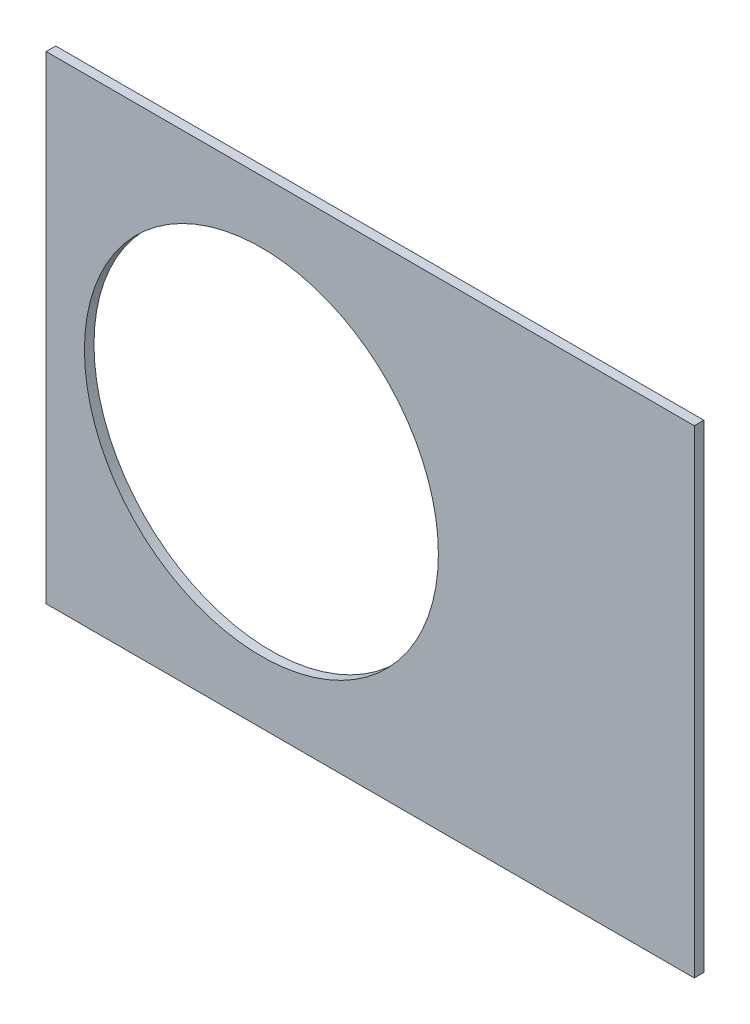
SolidWorks part; units mm, degrees
material "Copper"
ref_plane "Front Plane" through (0, 0, 0) normal (0, 0, 1) x (1, 0, 0)
ref_plane "Top Plane" through (0, 0, 0) normal (0, 1, 0) x (1, 0, 0)
ref_plane "Right Plane" through (0, 0, 0) normal (1, 0, 0) x (0, 0, -1)
sketch "Sketch1" plane through (0, 0, 0) normal (0, 0, 1) x (1, 0, 0)
  line L0 (0, 0) -> (320.3893, 0) construction
  line L1 (0, 0) -> (155.5285, 155.5285) construction
  line L2 (67.2115, 76.1917) -> (8.6967, 17.6769)
  line L3 (8.6967, 17.6769) -> (7.229, 14.1336)
  line L4 (101.4014, -6.35) -> (18.6489, -6.35)
  line L5 (15.1056, -4.8823) -> (18.6489, -6.35)
  line L6 (88.6729, 6.35) -> (27.8605, 6.35)
  line L9 (67.1914, 58.2111) -> (24.1905, 15.2102)
  line L10 (0, 0) -> (40.4486, 97.6516) construction
  line L11 (0, 0) -> (123.4567, -51.1374) construction
  line L18 (8.6967, 17.6769) -> (13.294, 8.6183) construction
  line L19 (18.6489, -6.35) -> (15.4943, 3.3063) construction
  line L20 (27.8605, 6.35) -> (27.7442, 6.7059) construction
  line L21 (24.1905, 15.2102) -> (24.3599, 14.8764) construction
  arc A0 (7.229, 14.1336) -> (15.1056, -4.8823) centre (0, 0) cw
  arc A1 (67.2115, 76.1917) -> (101.4014, -6.35) centre (0, 0) cw
  arc A2 (24.1905, 15.2102) -> (27.8605, 6.35) centre (0, 0) cw
  arc A3 (67.1914, 58.2111) -> (88.6729, 6.35) centre (0, 0) cw
  arc A8 (13.294, 8.6183) -> (15.4943, 3.3063) centre (0, 0) cw construction
  arc A9 (24.3599, 14.8764) -> (27.7442, 6.7059) centre (0, 0) cw construction
  dimension "D1" = 45
  dimension "D3" = 6.35
  dimension "D4" = 15.875
  dimension "D7" = 22.5
  dimension "D8" = 101.6
  dimension "D11" = 12.7
  dimension "D12" = 12.7
  dimension "D2" = 6.35
  dimension "D5" = 67.5
  dimension "D9" = 1.27
  dimension "D10" = 1.27
  dimension "D6" = 12.7
extrude "Boss-Extrude1" add sketch "Sketch1" along normal blind 0.254
sketch "Sketch2" plane through (0, 0, 0.254) normal (0, 0, 1) x (1, 0, 0)
  line L0 (0, 0) -> (101.6, 0) construction
  line L1 (0, 0) -> (71.842, 71.842) construction
  line L3 (0, 0) -> (22.225, 0) construction
  line L4 (0, 0) -> (15.7154, 15.7154) construction
  line L5 (0, 0) -> (95.25, 0) construction
  line L6 (0, 0) -> (92.0044, 24.6525) construction
  arc A0 (101.4014, -6.35) -> (67.2115, 76.1917) centre (0, 0) ccw construction
  circle A1 centre (22.225, 0) radius 4.699
  arc A2 (15.1056, -4.8823) -> (7.229, 14.1336) centre (0, 0) ccw construction
  circle A3 centre (36.195, 0) radius 4.699
  circle A4 centre (61.722, 0) radius 4.699
  circle A5 centre (75.692, 0) radius 4.699
  circle A6 centre (95.25, 0) radius 4.699
  circle A7 centre (15.7154, 15.7154) radius 4.699
  circle A8 centre (25.5937, 25.5937) radius 4.699
  circle A9 centre (43.644, 43.644) radius 4.699
  circle A10 centre (53.5223, 53.5223) radius 4.699
  circle A11 centre (92.0044, 24.6525) radius 4.699
  circle A12 centre (82.4889, 47.625) radius 4.699
  circle A13 centre (67.3519, 67.3519) radius 4.699
  dimension "D3" = 9.398
  dimension "D1" = 45
  dimension "D2" = 6.35
  dimension "D4" = 6.35
  dimension "D5" = 13.97
  dimension "D7" = 13.97
  dimension "D8" = 19.558
  dimension "D9" = 45
  dimension "D10" = 15
  dimension "D11" = 25.527
  dimension "D6" = 2
extrude "Cut-Extrude1" cut sketch "Sketch2" against normal through all
sketch "Sketch3" plane through (0, 0, 0.254) normal (0, 0, 1) x (1, 0, 0)
  line L0 (15.2664, 24.2467) -> (17.0625, 26.0427)
  line L1 (15.2664, 24.2467) -> (15.7154, 23.7977)
  line L2 (17.0625, 26.0427) -> (17.5115, 25.5937)
  line L3 (15.7154, 23.7977) -> (17.5115, 25.5937)
  line L4 (67.2115, 76.1917) -> (8.6967, 17.6769) construction
  line L5 (44.9911, 53.9713) -> (43.195, 52.1753)
  line L6 (44.9911, 53.9713) -> (45.4401, 53.5223)
  line L7 (43.195, 52.1753) -> (43.644, 51.7263)
  line L8 (45.4401, 53.5223) -> (43.644, 51.7263)
  line L9 (27.94, -6.35) -> (30.48, -6.35)
  line L10 (27.94, -6.35) -> (27.94, -5.715)
  line L11 (30.48, -6.35) -> (30.48, -5.715)
  line L12 (27.94, -5.715) -> (30.48, -5.715)
  line L13 (18.6489, -6.35) -> (101.4014, -6.35) construction
  line L14 (67.437, -6.35) -> (69.977, -6.35)
  line L15 (67.437, -6.35) -> (67.437, -5.715)
  line L16 (69.977, -6.35) -> (69.977, -5.715)
  line L17 (67.437, -5.715) -> (69.977, -5.715)
  line L18 (29.2307, 38.211) -> (31.0268, 40.007)
  line L19 (29.2307, 38.211) -> (29.6797, 37.762)
  line L20 (31.0268, 40.007) -> (31.4758, 39.558)
  line L21 (29.6797, 37.762) -> (31.4758, 39.558)
  line L22 (56.845, 65.8253) -> (55.049, 64.0292)
  line L23 (56.845, 65.8253) -> (57.294, 65.3763)
  line L24 (55.049, 64.0292) -> (55.498, 63.5802)
  line L25 (57.294, 65.3763) -> (55.498, 63.5802)
  line L26 (47.6885, -6.35) -> (50.2285, -6.35)
  line L27 (47.6885, -6.35) -> (47.6885, -5.715)
  line L28 (50.2285, -6.35) -> (50.2285, -5.715)
  line L29 (47.6885, -5.715) -> (50.2285, -5.715)
  line L30 (84.201, -6.35) -> (86.741, -6.35)
  line L31 (84.201, -6.35) -> (84.201, -5.715)
  line L32 (86.741, -6.35) -> (86.741, -5.715)
  line L33 (84.201, -5.715) -> (86.741, -5.715)
  line L34 (0, 0) -> (100.7308, 13.2615) construction
  line L35 (0, 0) -> (93.8662, 38.8806) construction
  line L36 (0, 0) -> (80.6047, 61.8502) construction
  line L37 (0, 0) -> (101.6, 0) construction
  line L38 (99.9355, 14.4377) -> (100.267, 11.9194)
  line L39 (99.9355, 14.4377) -> (101.1946, 14.6035)
  line L40 (100.267, 11.9194) -> (101.5261, 12.0852)
  line L41 (101.1946, 14.6035) -> (101.5261, 12.0852)
  line L42 (99.9355, 14.4377) -> (101.5261, 12.0852) construction
  line L43 (100.267, 11.9194) -> (101.1946, 14.6035) construction
  line L44 (93.7655, 37.4643) -> (94.9388, 37.9503)
  line L45 (93.7655, 37.4643) -> (92.7935, 39.811)
  line L46 (94.9388, 37.9503) -> (93.9668, 40.297)
  line L47 (92.7935, 39.811) -> (93.9668, 40.297)
  line L48 (93.7655, 37.4643) -> (93.9668, 40.297) construction
  line L49 (94.9388, 37.9503) -> (92.7935, 39.811) construction
  line L50 (79.3278, 62.4712) -> (80.874, 60.456)
  line L51 (79.3278, 62.4712) -> (80.3354, 63.2443)
  line L52 (80.874, 60.456) -> (81.8816, 61.2292)
  line L53 (80.3354, 63.2443) -> (81.8816, 61.2292)
  line L54 (79.3278, 62.4712) -> (81.8816, 61.2292) construction
  line L55 (80.874, 60.456) -> (80.3354, 63.2443) construction
  line L56 (13.5939, 7.0054) -> (14.5659, 4.6588)
  line L57 (13.5939, 7.0054) -> (14.7672, 7.4914)
  line L58 (14.5659, 4.6588) -> (15.7393, 5.1448)
  line L59 (14.7672, 7.4914) -> (15.7393, 5.1448)
  line L60 (13.5939, 7.0054) -> (15.7393, 5.1448) construction
  line L61 (14.5659, 4.6588) -> (14.7672, 7.4914) construction
  circle A0 centre (15.7154, 15.7154) radius 4.699 construction
  circle A1 centre (43.644, 43.644) radius 4.699 construction
  circle A2 centre (22.225, 0) radius 4.699 construction
  circle A3 centre (61.722, 0) radius 4.699 construction
  arc A4 (101.4014, -6.35) -> (67.2115, 76.1917) centre (0, 0) ccw construction
  arc A9 (15.1056, -4.8823) -> (7.229, 14.1336) centre (0, 0) ccw construction
  circle A10 centre (36.195, 0) radius 4.699 construction
  circle A11 centre (75.692, 0) radius 4.699 construction
  circle A12 centre (25.5937, 25.5937) radius 4.699 construction
  circle A13 centre (53.5223, 53.5223) radius 4.699 construction
  point P75 (14.6666, 6.0751)
  dimension "D2" = 5.715
  dimension "D3" = 2.54
  dimension "D6" = 5.715
  dimension "D8" = 0.635
  dimension "D9" = 5.715
  dimension "D12" = 5.715
  dimension "D4" = 7.5
  dimension "D5" = 22.5
  dimension "D7" = 37.5
  dimension "D10" = 90
  dimension "D11" = 1.27
  dimension "D14" = 0.635
  dimension "D15" = 90
  dimension "D18" = 0.635
  dimension "D19" = 90
  dimension "D22" = 0.635
  dimension "D20" = 1.27
  dimension "D17" = 0.635
  dimension "D13" = 11.4935
  dimension "D16" = 8.509
  dimension "D21" = 11.4935
  dimension "D23" = 8.509
extrude "Cut-Extrude2" cut sketch "Sketch3" against normal through all
sketch "Sketch5" plane through (0, 0, 0.254) normal (0, 0, 1) x (1, 0, 0)
  line L0 (27.8605, 6.35) -> (88.6729, 6.35) construction
  line L1 (30.48, -7.62) -> (47.6885, -7.62)
  line L2 (30.48, -7.62) -> (30.48, 7.62)
  line L3 (27.94, -5.715) -> (27.94, -6.35) construction
  line L4 (30.48, 7.62) -> (47.6885, 7.62)
  line L5 (47.6885, -7.62) -> (47.6885, 7.62)
  line L8 (30.48, -6.35) -> (47.6885, -6.35) construction
  line L10 (50.2285, -6.35) -> (50.2285, -5.715) construction
  dimension "D1" = 1.27
  dimension "D2" = 1.27
  dimension "D3" = 2.54
  dimension "D4" = 2.54
extrude "Cut-Extrude5" cut sketch "Sketch5" against normal through all flip side to cut
equation "\"cSep\"= 1.005"
equation "\"D11@Sketch2\"=\"cSep\""
equation "\"cSep2\"= \"D8@Sketch2\""
equation "\"D13@Sketch3\"=\"cSep\"/2-.05"
equation "\"D16@Sketch3\"=\"cSep2\"/2-.05"
equation "\"D21@Sketch3\"=\"cSep\"/2-.05"
equation "\"D23@Sketch3\"=\"cSep2\"/2-.05"
